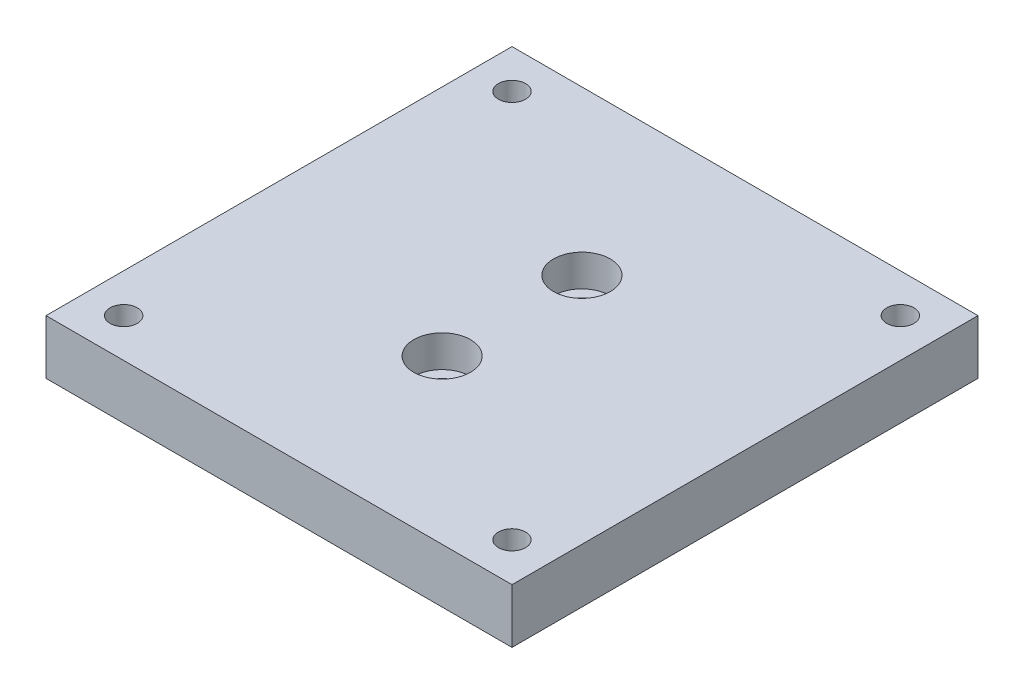
SolidWorks part; units mm, degrees
ref_plane "前基準面" through (0, 0, 0) normal (0, 0, 1) x (1, 0, 0)
ref_plane "上基準面" through (0, 0, 0) normal (0, 1, 0) x (1, 0, 0)
ref_plane "右基準面" through (0, 0, 0) normal (1, 0, 0) x (0, 0, -1)
sketch "草圖2" plane through (0, 0, 0) normal (0, 1, 0) x (1, 0, 0)
  line L1 (-30, 30) -> (30, 30)
  line L2 (-30, 30) -> (-30, -30)
  line L3 (-30, -30) -> (30, -30)
  line L4 (30, 30) -> (30, -30)
  line L5 (-30, 30) -> (30, -30) construction
  line L6 (-30, -30) -> (30, 30) construction
  point P0 (0, 0)
  dimension "D1" = 60
  dimension "D2" = 60
extrude "填料-伸長1" add sketch "草圖2" along normal blind 7
sketch "草圖3" plane through (0, 0, 0) normal (0, -1, 0) x (1, 0, 0)
  line L0 (0, 0) -> (0, 9.5171) construction
  line L1 (-21.8246, 25) -> (-23.4123, 27.75)
  line L2 (-23.4123, 27.75) -> (-26.5877, 27.75)
  line L3 (-26.5877, 27.75) -> (-28.1754, 25)
  line L4 (-28.1754, 25) -> (-26.5877, 22.25)
  line L5 (-26.5877, 22.25) -> (-23.4123, 22.25)
  line L6 (-23.4123, 22.25) -> (-21.8246, 25)
  line L7 (0, -5.5) -> (0, 5.5) construction
  line L8 (0, 0) -> (6.6459, 0) construction
  line L9 (5.5, 0) -> (-5.5, 0) construction
  line L10 (23.4123, 22.25) -> (21.8246, 25)
  line L11 (26.5877, 22.25) -> (23.4123, 22.25)
  line L12 (28.1754, 25) -> (26.5877, 22.25)
  line L13 (26.5877, 27.75) -> (28.1754, 25)
  line L14 (23.4123, 27.75) -> (26.5877, 27.75)
  line L15 (21.8246, 25) -> (23.4123, 27.75)
  line L16 (21.8246, -25) -> (23.4123, -27.75)
  line L17 (23.4123, -27.75) -> (26.5877, -27.75)
  line L18 (26.5877, -27.75) -> (28.1754, -25)
  line L19 (28.1754, -25) -> (26.5877, -22.25)
  line L20 (26.5877, -22.25) -> (23.4123, -22.25)
  line L21 (23.4123, -22.25) -> (21.8246, -25)
  line L22 (-23.4123, -22.25) -> (-21.8246, -25)
  line L23 (-26.5877, -22.25) -> (-23.4123, -22.25)
  line L24 (-28.1754, -25) -> (-26.5877, -22.25)
  line L25 (-26.5877, -27.75) -> (-28.1754, -25)
  line L26 (-23.4123, -27.75) -> (-26.5877, -27.75)
  line L27 (-21.8246, -25) -> (-23.4123, -27.75)
  circle A0 centre (-25, 25) radius 2.75 construction
  circle A1 centre (25, 25) radius 2.75 construction
  circle A2 centre (25, -25) radius 2.75 construction
  circle A3 centre (-25, -25) radius 2.75 construction
  dimension "D1" = 5.5
  dimension "D2" = 50
  dimension "D3" = 50
extrude "除料-伸長1" cut sketch "草圖3" against normal blind 2.6
sketch "草圖4" plane through (0, 7, 0) normal (0, 1, 0) x (1, 0, 0)
  line L0 (0, 0) -> (0, 11.1129) construction
  line L1 (0, -5.5) -> (0, 5.5) construction
  line L2 (0, 0) -> (9.6965, 0) construction
  line L3 (-5.5, 0) -> (5.5, 0) construction
  circle A0 centre (-25, 25) radius 1.75
  circle A1 centre (25, 25) radius 1.75
  circle A2 centre (25, -25) radius 1.75
  circle A3 centre (-25, -25) radius 1.75
  dimension "D1" = 3.5
  dimension "D2" = 50
  dimension "D3" = 50
extrude "除料-伸長2" cut sketch "草圖4" against normal up to next
sketch "草圖5" plane through (0, 7, 0) normal (0, 1, 0) x (1, 0, 0)
  line L0 (0, -5.5) -> (0, 5.5) construction
  line L1 (0, 0) -> (6.9728, 0) construction
  line L2 (-5.5, 0) -> (5.5, 0) construction
  circle A0 centre (0, 9) radius 3.65
  circle A1 centre (0, -9) radius 3.65
  dimension "D1" = 7.3
  dimension "D2" = 18
extrude "除料-伸長3" cut sketch "草圖5" against normal blind 4.1
sketch "草圖6" plane through (0, 2.9, 0) normal (0, 1, 0) x (1, 0, 0)
  circle A0 centre (0, 9) radius 2.25
  circle A1 centre (0, -9) radius 2.25
  dimension "D1" = 4.5
extrude "除料-伸長4" cut sketch "草圖6" against normal up to next
